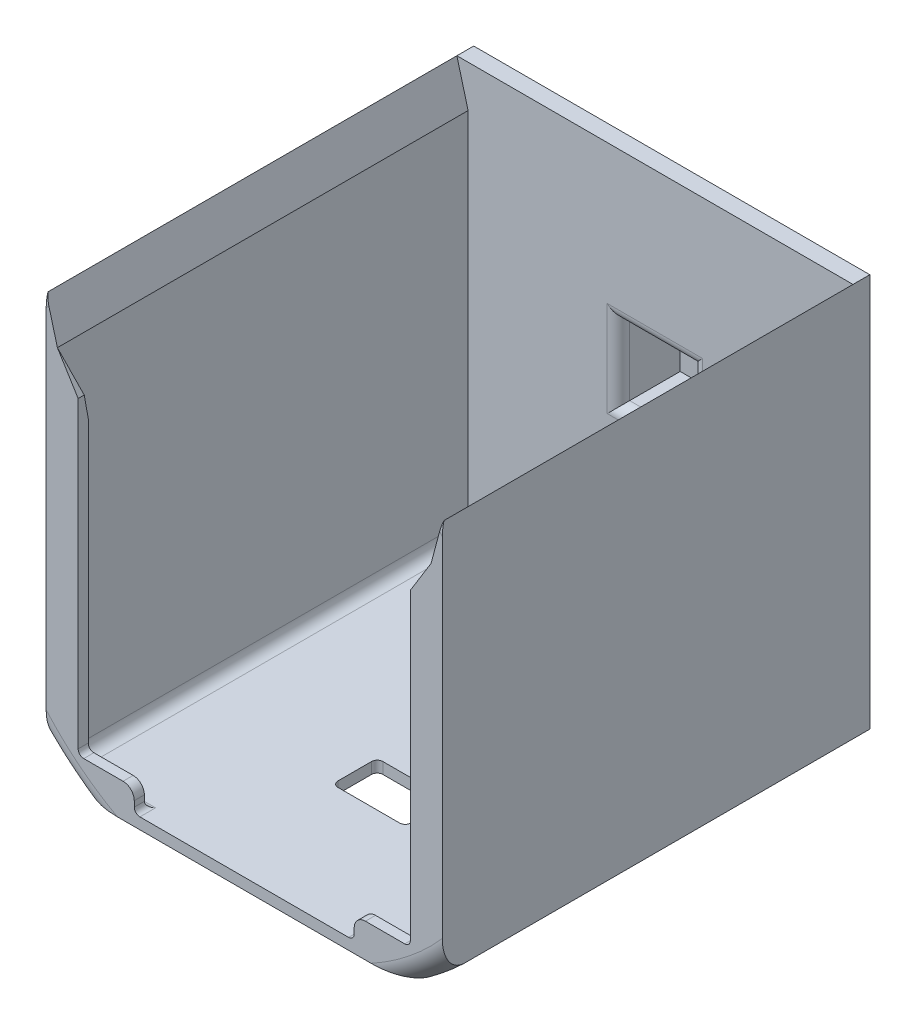
SolidWorks part; units mm, degrees
ref_plane "Front Plane" through (0, 0, 0) normal (0, 0, 1) x (1, 0, 0)
ref_plane "Top Plane" through (0, 0, 0) normal (0, 1, 0) x (1, 0, 0)
ref_plane "Right Plane" through (0, 0, 0) normal (1, 0, 0) x (0, 0, -1)
sketch "Sketch1" plane through (0, 0, 0) normal (0, 0, 1) x (1, 0, 0)
  circle A0 centre (0, 0) radius 5.8
  dimension "D1" = 11.6
extrude "Boss-Extrude1" add sketch "Sketch1" along normal blind 0.5
sketch "Sketch2" plane through (0, 0, 0.5) normal (0, 0, 1) x (1, 0, 0)
  circle A0 centre (0, 0) radius 25.5
  dimension "D1" = 51
extrude "Boss-Extrude2" add sketch "Sketch2" along normal offset from surface (38.1 mm away) 0.4 contours A0
sketch "Sketch3" plane through (0, 0, 0) normal (0, 0, -1) x (-1, 0, 0)
  circle A0 centre (0, 0) radius 4.975
  circle A1 centre (0, 0) radius 5 construction
  dimension "D1" = 0.025
extrude "Boss-Extrude3" add sketch "Sketch3" along normal up to surface (4 mm away)
sketch "Sketch4" plane through (0, 0, -4) normal (0, 0, -1) x (-1, 0, 0)
  line L0 (0, 0) -> (0, -4.975) construction
  line L2 (1.25, -2.6997) -> (-1.25, -2.6997) construction
  line L3 (1.25, -2.6997) -> (1.25, -4.2969)
  line L5 (-1.25, -2.6997) -> (-1.25, -4.2969)
  circle A0 centre (0, 0) radius 2.975 construction
  circle A1 centre (0, 0) radius 4.975 construction
  arc A2 (-1.25, -2.6997) -> (1.25, -2.6997) centre (0, 0) cw
  arc A3 (-1.25, -4.2969) -> (1.25, -4.2969) centre (0, 0) ccw
  point P11 (0, -2.6997)
  dimension "D1" = 2
  dimension "D3" = 0.5
  dimension "D2" = 2.5
extrude "Boss-Extrude4" add sketch "Sketch4" along normal blind 5
sketch "Sketch5" plane through (0, 0, 39) normal (0, 0, 1) x (1, 0, 0)
  line L1 (18.8272, 21.0618) -> (16.65, 12.9366)
  line L2 (16.65, 12.9366) -> (16.65, -19.6) construction
  line L3 (16.65, -19.6) -> (-16.65, -19.6) construction
  line L4 (-16.65, -19.6) -> (-16.65, 12.9366) construction
  line L5 (-16.65, 12.9366) -> (-18.8272, 21.0618)
  line L7 (15.9, -19.6) -> (-15.9, -19.6) construction
  line L8 (-16.65, 12.9366) -> (-16.65, -18.6)
  line L9 (-15.65, -19.6) -> (15.65, -19.6)
  line L10 (16.65, 12.9366) -> (16.65, -18.6)
  line L11 (15.65, -18.6) -> (15.65, -19.6) construction
  line L12 (16.65, -18.6) -> (15.65, -18.6) construction
  line L13 (-16.65, -18.6) -> (-15.65, -18.6) construction
  line L14 (-15.65, -18.6) -> (-15.65, -19.6) construction
  arc A0 (18.8272, 21.0618) -> (-18.8272, 21.0618) centre (0, 0) ccw
  arc A2 (-16.65, -18.6) -> (-15.65, -19.6) centre (-15.65, -18.6) ccw
  arc A3 (15.65, -19.6) -> (16.65, -18.6) centre (15.65, -18.6) ccw
  dimension "D1" = 1
  dimension "D2" = 1
extrude "Cut-Extrude2" cut sketch "Sketch5" against normal offset from surface (37 mm away) 1
shell "Shell1" thickness 1
sketch "Sketch7" plane through (0, 0, -9) normal (0, 0, -1) x (-1, 0, 0)
  circle A0 centre (0, 0) radius 1
  arc A1 (1.25, -2.6997) -> (-1.25, -2.6997) centre (0, 0) ccw construction
  dimension "D1" = 2
extrude "Cut-Extrude3" cut sketch "Sketch7" against normal up to surface (11 mm away) contours A0
sketch "Sketch8" plane through (0, 0, 2) normal (0, 0, 1) x (1, 0, 0)
  circle A0 centre (0, 0) radius 1.5
  dimension "D1" = 3
extrude "Cut-Extrude4" cut sketch "Sketch8" against normal up to surface (6 mm away)
fillet "Fillet2" radius 0.5 4 edges at (1.25, -3.4983, -9) (0, -4.475, -9) (-1.25, -3.4983, -9) (0, 2.975, -9)
sketch "Sketch11" plane through (0, 0, 2) normal (0, 0, 1) x (1, 0, 0)
  line L1 (3.25, -3.25) -> (-3.25, -3.25)
  line L2 (3.25, -3.25) -> (3.25, 3.25)
  line L3 (3.25, 3.25) -> (-3.25, 3.25)
  line L4 (-3.25, -3.25) -> (-3.25, 3.25)
  line L5 (3.25, -3.25) -> (-3.25, 3.25) construction
  line L6 (3.25, 3.25) -> (-3.25, -3.25) construction
  point P0 (0, 0)
  dimension "D1" = 6.5
  dimension "D2" = 6.5
extrude "Cut-Extrude6" cut sketch "Sketch11" against normal blind 5.5
fillet "Fillet4" radius 1 4 edges at (0, -3.25, 2) (-3.25, 0, 2) (0, 3.25, 2) (3.25, 0, 2)
ref_plane "Plane1" through (0, 0, 0) normal (1, 0, 0) x (0, 0, -1)
sketch "Sketch20" plane through (0, 0, 38.6) normal (0, 0, 1) x (1, 0, 0)
  line L0 (15.65, -19.6) -> (-15.65, -19.6) construction
  line L1 (-16.65, 12.9366) -> (-15.9, 12.9366) construction
  line L2 (-16.65, 12.9366) -> (-16.65, -19.6) construction
  line L3 (-16.65, -19.6) -> (-15.9, -19.6) construction
  line L4 (-15.9, 12.9366) -> (-15.9, -19.6) construction
  line L6 (-15.9, 12.9366) -> (-14.8, 12.9366) construction
  line L7 (-15.9, 12.9366) -> (-15.9, -19.6) construction
  line L8 (-15.9, -19.6) -> (-14.8, -19.6) construction
  line L9 (-14.8, 12.9366) -> (-14.8, -19.6) construction
  line L11 (-14.8, -17.6) -> (-9.8, -17.6)
  line L12 (-9.8, -17.6) -> (-9.8, -19.6)
  line L13 (-9.8, -19.6) -> (-15.65, -19.6)
  line L14 (-16.65, -18.6) -> (-16.65, 12.9366)
  line L15 (-16.65, 12.9366) -> (-14.8, 9.9366)
  line L16 (-14.8, 9.9366) -> (-14.8, -17.6)
  arc A1 (-15.65, -19.6) -> (-16.65, -18.6) centre (-15.65, -18.6) cw
  dimension "D1" = 0.75
  dimension "D2" = 1.1
  dimension "D3" = 5
  dimension "D4" = 2
  dimension "D5" = 3
extrude "Boss-Extrude5" add sketch "Sketch20" against normal blind 0.9
mirror "Mirror2" about plane through (0, 0, 0) normal (1, 0, 0) of "Boss-Extrude5"
sketch "Sketch21" plane through (-14.8, 0, 0) normal (1, 0, 0) x (0, 0, -1)
  line L0 (-37.7, 7.9366) -> (-37.7, 12.9366)
  line L1 (-37.7, -17.6) -> (-37.7, 9.9366) construction
  line L2 (-37.7, 12.9366) -> (-38.6, 12.9366)
  line L3 (-38.6, 12.9366) -> (-37.7, 7.9366)
  line L4 (-37.7, 12.9366) -> (-38.6, 12.9366) construction
  line L5 (-37.7, 9.9366) -> (-38.6, 9.9366) construction
  line L6 (-38.6, -19.6) -> (-38.6, -17.6) construction
  dimension "D1" = 2
extrude "Cut-Extrude7" cut sketch "Sketch21" against normal up to surface and the other way up to surface
sketch "Sketch22" plane through (0, -19.6, 0) normal (0, 1, 0) x (1, 0, 0)
  line L0 (3.25, -27.5) -> (-3.25, -23.5) construction
  line L1 (3.25, -27.5) -> (-3.25, -27.5)
  line L2 (3.25, -27.5) -> (3.25, -23.5)
  line L3 (3.25, -23.5) -> (-3.25, -23.5)
  line L4 (-3.25, -27.5) -> (-3.25, -23.5)
  line L5 (-3.25, -27.5) -> (3.25, -23.5) construction
  line L6 (0, -38.6) -> (0, -25.5) construction
  line L7 (9.8, -38.6) -> (-9.8, -38.6) construction
  line L8 (-26.75, -39) -> (6.212, -39) construction
  dimension "D1" = 13.5
  dimension "D2" = 4
  dimension "D3" = 6.5
extrude "Cut-Extrude8" cut sketch "Sketch22" against normal up to surface (1 mm away)
fillet "Fillet6" radius 2 1 edges at (0, -25.5, 38.6)
sketch "Sketch25" plane through (-16.65, 0, 0) normal (1, 0, 0) x (0, 0, -1)
  line L0 (-2, -18.6) -> (-37.7, -18.6) construction
  line L1 (-31.7, 6.9366) -> (-8, 6.9366)
  line L2 (-31.7, 6.9366) -> (-31.7, -12.6)
  line L3 (-31.7, -12.6) -> (-8, -12.6)
  line L4 (-8, 6.9366) -> (-8, -12.6)
  line L5 (-2, 12.9366) -> (-38.6, 12.9366) construction
  line L7 (-37.7, 7.9366) -> (-37.7, -18.6) construction
  line L8 (-2, 12.9366) -> (-2, -18.6) construction
  dimension "D1" = 6
  dimension "D2" = 6
  dimension "D3" = 6
  dimension "D4" = 6
extrude "Cut-Extrude10" [suppressed] cut sketch "Sketch25" along normal through all and the other way through all
sketch "Sketch26" plane through (0, -19.6, 0) normal (0, 1, 0) x (1, 0, 0)
  line L0 (-15.65, -2) -> (15.65, -2) construction
  line L1 (-9.65, -8) -> (9.65, -8)
  line L2 (-9.65, -8) -> (-9.65, -19.5)
  line L3 (-9.65, -19.5) -> (9.65, -19.5)
  line L4 (9.65, -8) -> (9.65, -19.5)
  line L5 (3.25, -23.5) -> (-3.25, -23.5) construction
  line L6 (-15.65, -2) -> (-15.65, -37.7) construction
  line L7 (15.65, -2) -> (15.65, -37.7) construction
  dimension "D1" = 6
  dimension "D2" = 4
  dimension "D3" = 6
  dimension "D4" = 6
extrude "Cut-Extrude11" [suppressed] cut sketch "Sketch26" against normal through all
sketch "Sketch30" plane through (0, -20.6, 0) normal (0, -1, 0) x (1, 0, 0)
  line L0 (-23.9112, 46.7698) -> (22.1581, 46.7698)
  line L1 (-23.9112, 46.7698) -> (-23.9112, -15.7283)
  line L2 (22.1581, 46.7698) -> (22.1581, -15.7283)
  line L3 (-23.9112, -15.7283) -> (22.1581, -15.7283)
extrude "Cut-Extrude13" cut sketch "Sketch30" along normal through all
sketch "Sketch31" plane through (-17.65, 0, 0) normal (-1, 0, 0) x (0, 0, 1)
  line L0 (-26.7725, 19.3954) -> (45.7447, 19.3954)
  line L1 (-26.7725, 19.3954) -> (-26.7725, -37.9719)
  line L2 (45.7447, 19.3954) -> (45.7447, -37.9719)
  line L3 (-26.7725, -37.9719) -> (45.7447, -37.9719)
extrude "Cut-Extrude14" cut sketch "Sketch31" along normal through all
sketch "Sketch32" plane through (17.65, 0, 0) normal (1, 0, 0) x (0, 0, -1)
  line L0 (0, 20.2973) -> (1.05, -40.5853)
  line L1 (0, 20.2973) -> (-59.7438, 19.267)
  line L2 (1.05, -40.5853) -> (-58.6937, -41.6157)
  line L3 (-59.7438, 19.267) -> (-58.6937, -41.6157)
extrude "Cut-Extrude15" cut sketch "Sketch32" along normal through all
ref_plane "Plane2" through (0, 16.6686, 0) normal (0, -1, 0) x (-1, 0, 0)
sketch "Sketch33" plane through (0, 16.6686, 0) normal (0, -1, 0) x (-1, 0, 0)
  line L0 (21.1415, 8.0762) -> (-21.4896, 8.0762)
  line L1 (21.1415, 8.0762) -> (21.1415, -47.8155)
  line L2 (-21.4896, 8.0762) -> (-21.4896, -47.8155)
  line L3 (21.1415, -47.8155) -> (-21.4896, -47.8155)
extrude "Cut-Extrude16" cut sketch "Sketch33" against normal through all
fillet "Fillet7" radius 1 2 edges at (9.8, -17.6, 38.15) (-9.8, -17.6, 38.15)
fillet "Fillet8" radius 0.5 14 edges at (12.725, -19.6, 37.7) (16.3571, -19.3071, 37.7) (-12.725, -19.6, 37.7) (-16.3571, -19.3071, 37.7) (-14.8, -17.6, 38.15) (14.8, -17.6, 38.15) (9.8, -19.6, 38.15) (-9.8, -19.6, 38.15) (16.65, -5.3317, 37.7) (-16.65, -5.3317, 37.7) (3.25, -20.1, 27.5) (3.25, -20.1, 23.5) (-3.25, -20.1, 27.5) (-3.25, -20.1, 23.5)
sketch "Sketch34" plane through (0, 0, -4) normal (0, 0, -1) x (-1, 0, 0)
  line L1 (-8.9364, 8.7929) -> (8.9364, 8.7929)
  line L2 (-8.9364, 8.7929) -> (-8.9364, -8.7929)
  line L3 (-8.9364, -8.7929) -> (8.9364, -8.7929)
  line L4 (8.9364, 8.7929) -> (8.9364, -8.7929)
  line L5 (-8.9364, 8.7929) -> (8.9364, -8.7929) construction
  line L6 (-8.9364, -8.7929) -> (8.9364, 8.7929) construction
  point P0 (0, 0)
extrude "Cut-Extrude17" cut sketch "Sketch34" along normal through all
sketch "Sketch35" plane through (0, 0, 0.5) normal (0, 0, -1) x (-1, 0, 0)
  line L0 (-3.25, 3.25) -> (3.25, 3.25) construction
  line L1 (-3.95, 3.95) -> (3.95, 3.95)
  line L2 (-3.95, 3.95) -> (-3.95, -3.95)
  line L3 (-3.95, -3.95) -> (3.95, -3.95)
  line L4 (3.95, 3.95) -> (3.95, -3.95)
  line L5 (-3.95, 3.95) -> (3.95, -3.95) construction
  line L6 (-3.95, -3.95) -> (3.95, 3.95) construction
  line L7 (-3.25, -3.25) -> (-3.25, 3.25) construction
  point P0 (0, 0)
  dimension "D1" = 0.7
  dimension "D2" = 0.7
extrude "Cut-Extrude18" cut sketch "Sketch35" along normal through all flip side to cut
ref_plane "GROUND PLANE" through (0, 0, 39) normal (0, 0, 1) x (1, 0, 0)
equation "\"D2@Sketch5\"=\"D1@Sketch5\""
equation "\"D2@Sketch27\"=\"D1@Sketch27\""
